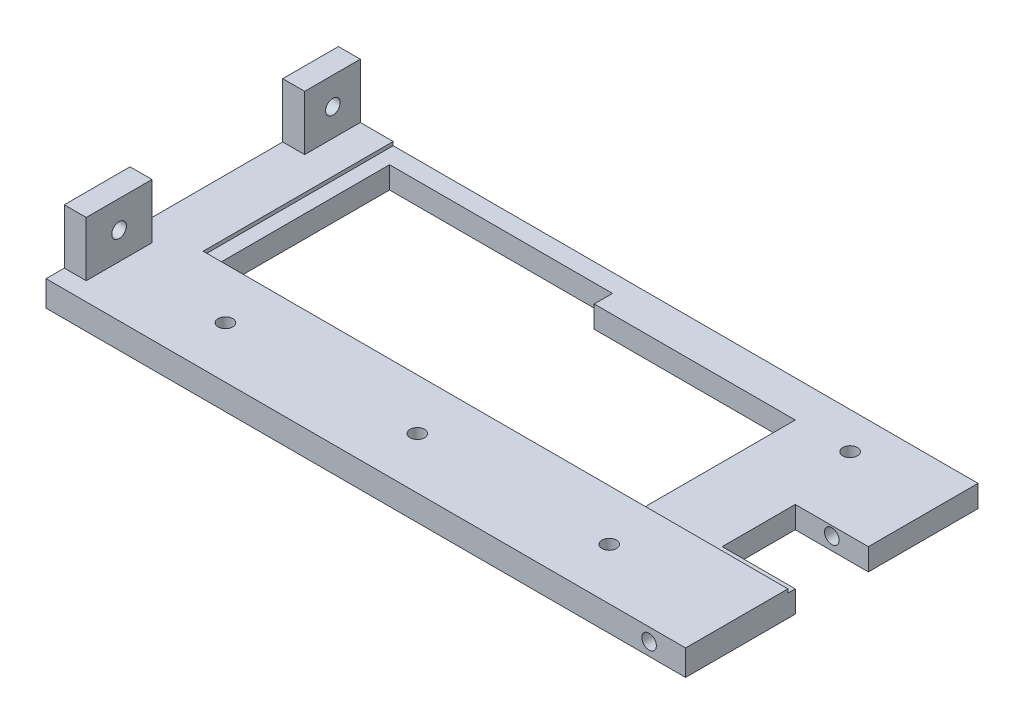
SolidWorks part; units mm, degrees
ref_plane "Front Plane" through (0, 0, 0) normal (0, 0, 1) x (1, 0, 0)
ref_plane "Top Plane" through (0, 0, 0) normal (0, 1, 0) x (1, 0, 0)
ref_plane "Right Plane" through (0, 0, 0) normal (1, 0, 0) x (0, 0, -1)
sketch "Sketch1" plane through (0, 0, 0) normal (0, 1, 0) x (1, 0, 0)
  line L1 (-89.8834, 33.007) -> (85.1166, 33.007)
  line L2 (-89.8834, 33.007) -> (-89.8834, -46.993)
  line L3 (-89.8834, -46.993) -> (85.1166, -46.993)
  line L4 (85.1166, 33.007) -> (85.1166, -46.993)
  dimension "D1" = 80
  dimension "D2" = 175
extrude "Boss-Extrude1" add sketch "Sketch1" along normal blind 7
sketch "Sketch2" plane through (0, 7, 0) normal (0, 1, 0) x (1, 0, 0)
  line L0 (-89.8834, -46.993) -> (85.1166, -46.993) construction
  line L1 (-89.8834, 33.007) -> (-89.8834, -46.993) construction
  line L2 (85.1166, -46.993) -> (85.1166, 33.007) construction
  circle A0 centre (-54.8834, -32.893) radius 2
  circle A1 centre (-2.3834, -32.893) radius 2
  circle A2 centre (50.1166, -32.893) radius 2
  dimension "D1" = 14.1
  dimension "D2" = 14.1
  dimension "D3" = 14.1
  dimension "D4" = 35
  dimension "D5" = 52.5
  dimension "D6" = 52.5
  dimension "D7" = 35
extrude "Cut-Extrude1" cut sketch "Sketch2" against normal blind 10
sketch "Sketch3" plane through (0, 7, 0) normal (0, 1, 0) x (1, 0, 0)
  line L0 (85.1166, -46.993) -> (85.1166, 33.007) construction
  line L1 (85.1166, -18.993) -> (-74.8834, -18.993)
  line L2 (85.1166, -18.993) -> (85.1166, 33.007)
  line L3 (85.1166, 33.007) -> (-74.8834, 33.007)
  line L4 (-74.8834, -18.993) -> (-74.8834, 33.007)
  line L5 (85.1166, 33.007) -> (-89.8834, 33.007) construction
  line L6 (-89.8834, -46.993) -> (85.1166, -46.993) construction
  dimension "D1" = 160
  dimension "D2" = 28
extrude "Cut-Extrude2" cut sketch "Sketch3" against normal blind 1
sketch "Sketch6" plane through (0, 6, 0) normal (0, 1, 0) x (1, 0, 0)
  line L0 (-74.8834, -18.993) -> (85.1166, -18.993) construction
  line L2 (-70.8834, 23.007) -> (-70.8834, -18.993)
  line L3 (-70.8834, -18.993) -> (45.1166, -18.993)
  line L4 (45.1166, 23.007) -> (45.1166, -18.993)
  line L5 (85.1166, -18.993) -> (85.1166, 33.007) construction
  line L6 (85.1166, 33.007) -> (-74.8834, 33.007) construction
  line L7 (-74.8834, 33.007) -> (-74.8834, -18.993) construction
  line L8 (-9.8834, 23.007) -> (45.1166, 23.007)
  line L10 (-70.8834, 23.007) -> (-70.8834, 28.007)
  line L11 (-70.8834, 28.007) -> (-9.8834, 28.007)
  line L12 (-9.8834, 23.007) -> (-9.8834, 28.007)
  dimension "40" = 40
  dimension "D2" = 4
  dimension "D3" = 5
  dimension "D4" = 95
extrude "Cut-Extrude3" cut sketch "Sketch6" against normal blind 10
sketch "Sketch7" plane through (0, 7, 0) normal (0, 1, 0) x (1, 0, 0)
  line L0 (-89.8834, 33.007) -> (-89.8834, -46.993) construction
  line L1 (-89.8834, 33.007) -> (-83.8834, 33.007)
  line L2 (-89.8834, 33.007) -> (-89.8834, 17.7803)
  line L3 (-89.8834, 17.7803) -> (-83.8834, 17.7803)
  line L4 (-83.8834, 33.007) -> (-83.8834, 17.7803)
  line L5 (-89.8834, -41.993) -> (-83.8834, -41.993)
  line L6 (-89.8834, -41.993) -> (-89.8834, -23.993)
  line L7 (-89.8834, -23.993) -> (-83.8834, -23.993)
  line L8 (-83.8834, -41.993) -> (-83.8834, -23.993)
  line L9 (-89.8834, -46.993) -> (85.1166, -46.993) construction
  dimension "D1" = 6
  dimension "D2" = 15.2267
  dimension "D3" = 5
  dimension "D4" = 18
  dimension "D5" = 6
extrude "Boss-Extrude3" add sketch "Sketch7" along normal blind 15
sketch "Sketch8" plane through (-83.8834, 0, 0) normal (1, 0, 0) x (0, 0, -1)
  line L0 (33.007, 22) -> (33.007, 7) construction
  line L1 (17.7803, 22) -> (33.007, 22) construction
  line L2 (-23.993, 22) -> (-23.993, 7) construction
  circle A0 centre (25.507, 14.5) radius 2
  circle A1 centre (-32.993, 14.5) radius 2
  dimension "D1" = 7.5
  dimension "D3" = 9
  dimension "D2" = 7.5
extrude "Cut-Extrude4" cut sketch "Sketch8" against normal blind 15
sketch "Sketch9" plane through (0, 0, 0) normal (0, -1, 0) x (1, 0, 0)
  line L0 (85.1166, 46.993) -> (85.1166, -33.007) construction
  line L1 (85.1166, 16.993) -> (65.1166, 16.993)
  line L2 (85.1166, 16.993) -> (85.1166, -3.007)
  line L3 (85.1166, -3.007) -> (65.1166, -3.007)
  line L4 (65.1166, 16.993) -> (65.1166, -3.007)
  line L5 (-89.8834, 46.993) -> (85.1166, 46.993) construction
  line L6 (85.1166, -33.007) -> (-89.8834, -33.007) construction
  dimension "D1" = 20
  dimension "D2" = 20
  dimension "D3" = 30
  dimension "D4" = 30
extrude "Cut-Extrude5" cut sketch "Sketch9" against normal blind 15
sketch "Sketch10" plane through (0, 0, -3.007) normal (0, 0, 1) x (1, 0, 0)
  line L0 (85.1166, 6) -> (85.1166, 0) construction
  line L1 (65.1166, 0) -> (85.1166, 0) construction
  circle A0 centre (75.1166, 3.5) radius 2
  dimension "D1" = 10
  dimension "D2" = 3.5
extrude "Cut-Extrude7" cut sketch "Sketch10" against normal through all both and the other way through all
sketch "Sketch11" plane through (0, 0, 0) normal (0, -1, 0) x (1, 0, 0)
  line L0 (85.1166, -33.007) -> (-89.8834, -33.007) construction
  line L1 (85.1166, -3.007) -> (85.1166, -33.007) construction
  circle A0 centre (60.1166, -23.007) radius 2
  dimension "D1" = 10
  dimension "D2" = 25
extrude "Cut-Extrude8" cut sketch "Sketch11" against normal blind 10 contours A0
